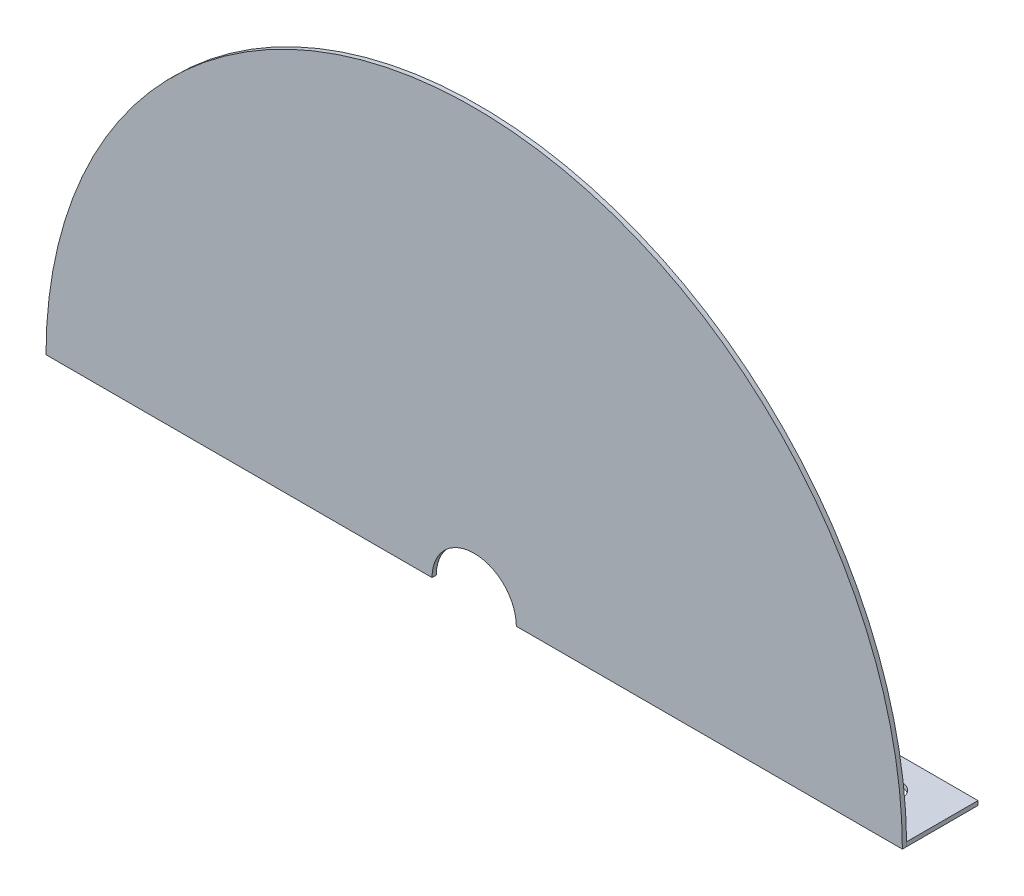
SolidWorks part; units mm, degrees
material "Plain Carbon Steel"
ref_plane "Front Plane" through (0, 0, 0) normal (0, 0, 1) x (1, 0, 0)
ref_plane "Top Plane" through (0, 0, 0) normal (0, 1, 0) x (1, 0, 0)
ref_plane "Right Plane" through (0, 0, 0) normal (1, 0, 0) x (0, 0, -1)
sketch "Plate shape" plane through (0, 0, 0) normal (0, 0, 1) x (1, 0, 0)
  line L3 (-154.3999, 0) -> (210.7061, 0) construction
  line L4 (0, 152.4) -> (-152.4, 152.4)
  line L5 (0, 152.4) -> (152.4, 152.4)
  line L9 (0, 152.4) -> (0, 0) construction
  line L10 (0, 152.4) -> (30, 152.4) construction
  line L11 (30, 152.4) -> (30, 301.8181) construction
  arc A0 (-152.4, 152.4) -> (152.4, 152.4) centre (0, 152.4) cw
  arc A1 (152.4, 152.4) -> (-152.4, 152.4) centre (0, 152.4) cw construction
  dimension "D1" = 152.4
  dimension "D2" = 30
extrude "Outer casing" add sketch "Plate shape" along normal blind 1.5189
sketch "Sketch1" plane through (0, 0, 1.5189) normal (0, 0, 1) x (1, 0, 0)
  circle A0 centre (0, 152.4) radius 152.4 construction
  arc A1 (152.4, 152.4) -> (-152.4, 152.4) centre (0, 152.4) ccw construction
  circle A2 centre (0, 152.4) radius 15
  dimension "D1" = 30
extrude "Inner Cutout" cut sketch "Sketch1" against normal blind 20
sketch "Sketch3" plane through (0, 0, 1.5189) normal (0, 0, 1) x (1, 0, 0)
  line L0 (30, 152.4) -> (30, 301.8181) construction
  line L1 (15, 152.4) -> (152.4, 152.4) construction
  line L2 (-15, 152.4) -> (15, 152.4) construction
  arc A0 (152.4, 152.4) -> (-152.4, 152.4) centre (0, 152.4) ccw construction
  point P11 (0, 152.4)
  dimension "D1" = 30
sketch "Sketch4" plane through (0, 0, 0) normal (0, 0, -1) x (-1, 0, 0)
  line L0 (-152.4, 152.4) -> (-76.2, 152.4)
  line L1 (-15, 152.4) -> (-152.4, 152.4) construction
  line L2 (-76.2, 152.4) -> (-76.2, 153.9189)
  line L3 (-76.2, 153.9189) -> (-152.4, 153.9189)
  line L4 (-152.4, 153.9189) -> (-152.4, 152.4)
  line L5 (152.4, 152.4) -> (76.2, 152.4)
  line L7 (152.4, 152.4) -> (15, 152.4) construction
  line L8 (76.2, 152.4) -> (76.2, 153.9189)
  line L9 (76.2, 153.9189) -> (152.4, 153.9189)
  line L10 (152.4, 153.9189) -> (152.4, 152.4)
  dimension "D1" = 1.5189
  dimension "D2" = 76.2
  dimension "D3" = 1.5189
  dimension "D4" = 76.2
extrude "Boss-Extrude1" add sketch "Sketch4" along normal blind 25.4
sketch "Sketch5" plane through (0, 153.9189, 0) normal (0, 1, 0) x (1, 0, 0)
  line L0 (152.4, 12.7) -> (76.2, 12.7) construction
  line L1 (152.4, 25.4) -> (152.4, 0) construction
  line L2 (76.2, 25.4) -> (76.2, 0) construction
  line L3 (0, -14.8054) -> (0, 14.8054) construction
  circle A0 centre (133.35, 12.7) radius 4.7625
  circle A1 centre (95.25, 12.7) radius 4.7625
  circle A2 centre (-133.35, 12.7) radius 4.7625
  circle A3 centre (-95.25, 12.7) radius 4.7625
  dimension "D3" = 9.525
  dimension "D1" = 38.1
  dimension "D2" = 19.05
extrude "Cut-Extrude1" cut sketch "Sketch5" against normal through all
